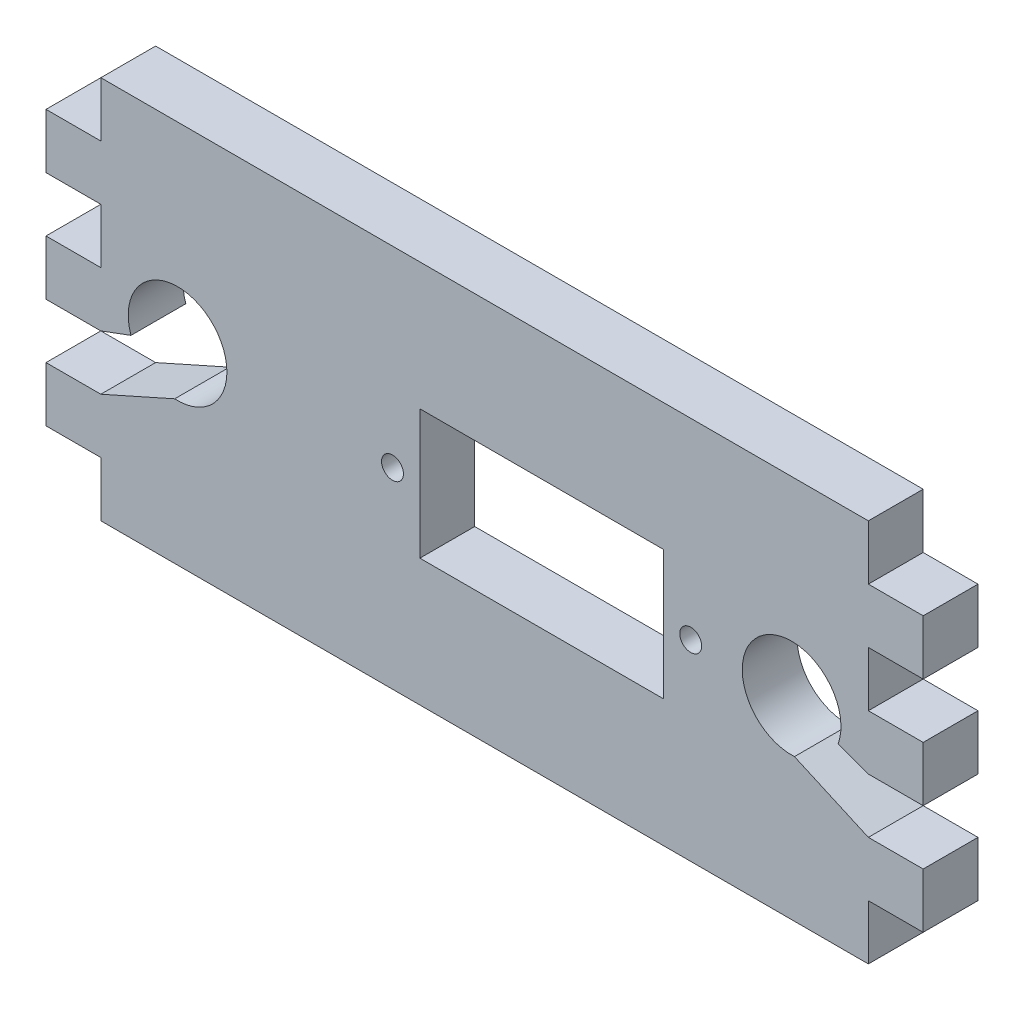
SolidWorks part; units mm, degrees
material "Balsa"
ref_plane "Plan de face" through (0, 0, 0) normal (0, 0, 1) x (1, 0, 0)
ref_plane "Plan de dessus" through (0, 0, 0) normal (0, 1, 0) x (1, 0, 0)
ref_plane "Plan de droite" through (0, 0, 0) normal (1, 0, 0) x (0, 0, -1)
sketch "Esquisse1" plane through (0, 0, 0) normal (0, 0, 1) x (1, 0, 0)
  line L1 (-40, 17.5) -> (40, 17.5)
  line L2 (-40, 17.5) -> (-40, -17.5)
  line L3 (-40, -17.5) -> (40, -17.5)
  line L4 (40, 17.5) -> (40, -17.5)
  dimension "D1" = 80
  dimension "D2" = 35
  dimension "D3" = 40
  dimension "D4" = 17.5
extrude "Boss.-Extru.1" add sketch "Esquisse1" along normal blind 5 contours L1 L4 L3 L2
sketch "Esquisse3" plane through (0, 0, 0) normal (0, 0, 1) x (1, 0, 0)
  line L0 (40, 17.5) -> (40, -17.5) construction
  line L1 (40, -12.5) -> (35, -12.5)
  line L2 (40, -12.5) -> (40, -17.5)
  line L3 (40, -17.5) -> (35, -17.5)
  line L4 (35, -12.5) -> (35, -17.5)
  line L5 (-40, -17.5) -> (40, -17.5) construction
  dimension "D1" = 5
  dimension "D2" = 5
extrude "Enlèv. mat.-Extru.1" cut sketch "Esquisse3" along normal blind 10
pattern_linear "Répétition linéaire1" count 4 spacing 10 along (0, 1, 0) of "Enlèv. mat.-Extru.1"
sketch "Esquisse4" plane through (0, 0, 0) normal (0, 0, 1) x (1, 0, 0)
  line L0 (-40, 17.5) -> (-40, -17.5) construction
  line L1 (-40, -12.5) -> (-35, -12.5)
  line L2 (-40, -12.5) -> (-40, -17.5)
  line L3 (-40, -17.5) -> (-35, -17.5)
  line L4 (-35, -12.5) -> (-35, -17.5)
  line L5 (-40, -17.5) -> (35, -17.5) construction
  dimension "D1" = 5
  dimension "D2" = 5
extrude "Enlèv. mat.-Extru.2" cut sketch "Esquisse4" along normal blind 10
pattern_linear "Répétition linéaire2" count 4 spacing 10 along (0, 1, 0) of "Enlèv. mat.-Extru.2"
sketch "Esquisse6" plane through (0, 0, 0) normal (0, 0, 1) x (1, 0, 0)
  line L1 (-5.9, 5.9) -> (16.3, 5.9)
  line L2 (-5.9, 5.9) -> (-5.9, -5.9)
  line L3 (-5.9, -5.9) -> (16.3, -5.9)
  line L4 (16.3, 5.9) -> (16.3, -5.9)
  dimension "D1" = 11.8
  dimension "D2" = 22.2
  dimension "D3" = 5.9
  dimension "D4" = 5.9
extrude "Enlèv. mat.-Extru.5" cut sketch "Esquisse6" along normal blind 10
sketch "Esquisse7" plane through (0, 0, 0) normal (0, 0, 1) x (1, 0, 0)
  line L0 (16.3, -5.9) -> (16.3, 5.9) construction
  line L1 (-5.9, -5.9) -> (-5.9, 5.9) construction
  circle A0 centre (18.8, 0) radius 1
  circle A1 centre (-8.4, 0) radius 0.9992
  point P2 (16.3, 0)
  dimension "D1" = 2.5
  dimension "D2" = 2.5
extrude "Enlèv. mat.-Extru.7" cut sketch "Esquisse7" along normal blind 10
sketch "Esquisse8" plane through (0, 0, 0) normal (0, 0, -1) x (-1, 0, 0)
  line L0 (35, -17.5) -> (-35, -17.5) construction
  line L1 (40, 2.5) -> (40, -2.5) construction
  circle A0 centre (28, 0) radius 4.5
  dimension "D3" = 9
  dimension "D1" = 17.5
  dimension "D2" = 12
extrude "Enlèv. mat.-Extru.8" cut sketch "Esquisse8" against normal blind 10
sketch "Esquisse9" plane through (0, 0, 0) normal (0, 0, -1) x (-1, 0, 0)
  line L0 (32.25, -1.479) -> (35, -2.5)
  line L1 (35, -2.5) -> (35, -7.5)
  line L2 (35, -7.5) -> (28.2601, -4.4925)
  line L3 (28.2601, -4.4925) -> (32.25, -1.479)
  circle A0 centre (28, 0) radius 4.5 construction
  dimension "D1" = 2.75
  dimension "D2" = 5
extrude "Enlèv. mat.-Extru.9" cut sketch "Esquisse9" against normal blind 10
mirror "Symétrie1" about plane through (0, 0, 0) normal (1, 0, 0) of "Enlèv. mat.-Extru.9", "Enlèv. mat.-Extru.8"
